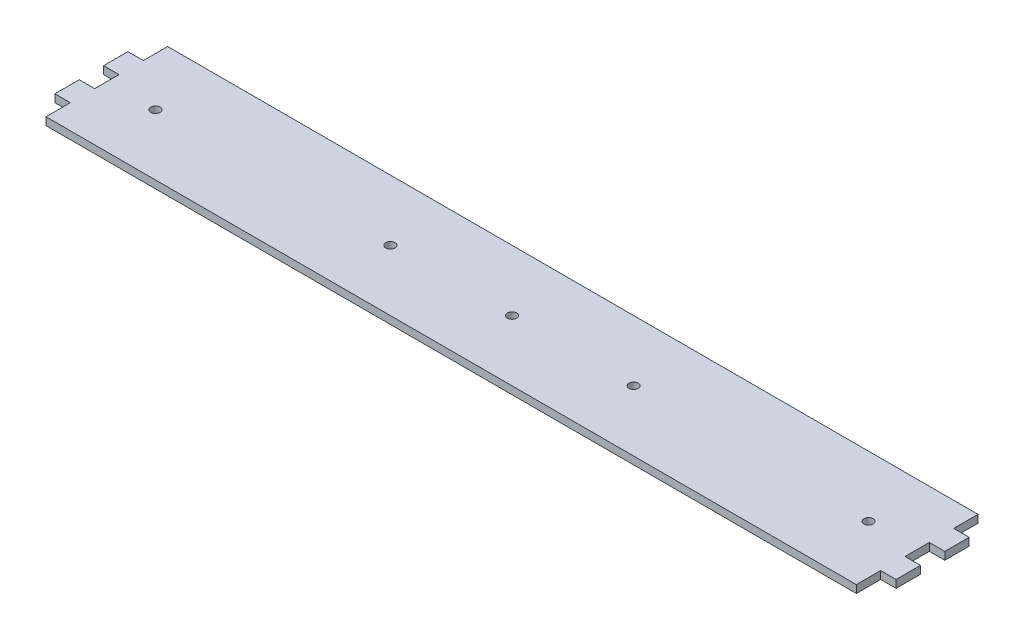
SolidWorks part; units mm, degrees
ref_plane "Front Plane" through (0, 0, 0) normal (0, 0, 1) x (1, 0, 0)
ref_plane "Top Plane" through (0, 0, 0) normal (0, 1, 0) x (1, 0, 0)
ref_plane "Right Plane" through (0, 0, 0) normal (1, 0, 0) x (0, 0, -1)
sketch "Sketch1" plane through (0, 0, 0) normal (0, 1, 0) x (1, 0, 0)
  line L0 (-166.5, 25) -> (-166.5, 15) construction
  line L1 (-166.5, -25) -> (166.5, -25)
  line L2 (-166.5, -25) -> (-166.5, 25)
  line L3 (-166.5, 25) -> (166.5, 25)
  line L4 (166.5, -25) -> (166.5, 25)
  line L5 (-166.5, -25) -> (166.5, 25) construction
  line L6 (-166.5, 25) -> (166.5, -25) construction
  line L7 (-166.5, 15) -> (-172.85, 15)
  line L8 (-172.85, 15) -> (-172.85, 5)
  line L9 (-172.85, 5) -> (-166.5, 5)
  line L10 (-166.5, 5) -> (-166.5, 15)
  line L11 (172.85, 15) -> (166.5, 15)
  line L12 (166.5, 15) -> (166.5, 5)
  line L13 (166.5, 5) -> (172.85, 5)
  line L14 (172.85, 5) -> (172.85, 15)
  line L15 (172.85, -5) -> (166.5, -5)
  line L16 (166.5, -5) -> (166.5, -15)
  line L17 (166.5, -15) -> (172.85, -15)
  line L18 (172.85, -15) -> (172.85, -5)
  line L19 (-166.5, -5) -> (-172.85, -5)
  line L20 (-172.85, -5) -> (-172.85, -15)
  line L21 (-172.85, -15) -> (-166.5, -15)
  line L22 (-166.5, -15) -> (-166.5, -5)
  line L23 (166.5, 0) -> (146.5, 0) construction
  line L24 (-166.5, 0) -> (-146.5, 0) construction
  circle A0 centre (0, 0) radius 1.9
  circle A1 centre (50, 0) radius 1.9
  circle A2 centre (-50, 0) radius 1.9
  circle A3 centre (146.5, 0) radius 1.9
  circle A4 centre (-146.5, 0) radius 1.9
  point P0 (0, 0)
  dimension "D5" = 2
  dimension "D7" = 3.8
  dimension "D1" = 50
  dimension "D2" = 333
  dimension "D3" = 2
  dimension "D4" = 2
  dimension "D6" = 2
extrude "Boss-Extrude1" add sketch "Sketch1" along normal blind 3.175 contours L8 L9 L2 L7 | L1 L4 L3 L2 | L17 L18 L15 L4 | L20 L21 L22 L19 | L14 L11 L12 L13
